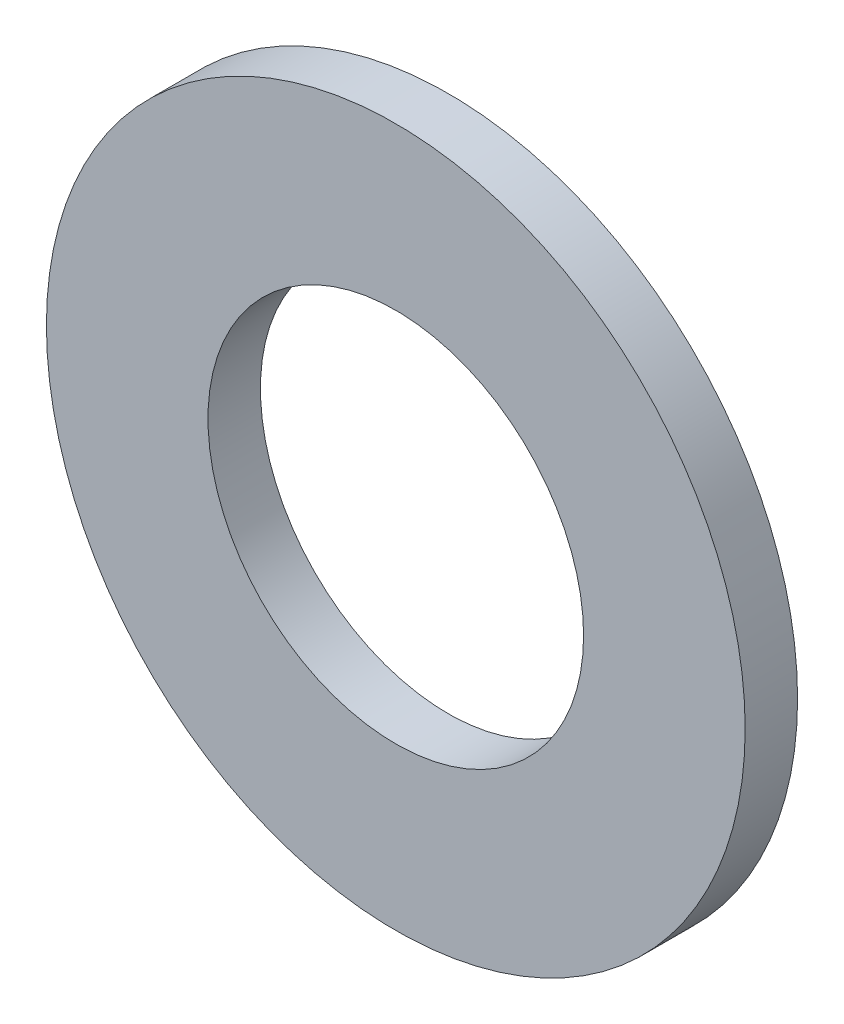
SolidWorks part; units mm, degrees
ref_plane "Front Plane" through (0, 0, 0) normal (0, 0, 1) x (1, 0, 0)
ref_plane "Top Plane" through (0, 0, 0) normal (0, 1, 0) x (1, 0, 0)
ref_plane "Right Plane" through (0, 0, 0) normal (1, 0, 0) x (0, 0, -1)
sketch "Sketch1" plane through (0, 0, 0) normal (0, 0, 1) x (1, 0, 0)
  circle A0 centre (0, 0) radius 4
  circle A1 centre (0, 0) radius 2.15
  point P5 (0, -4)
  dimension "OD" = 8
  dimension "ID" = 4.3
sketch "Sketch2" plane through (0, 0, 0) normal (1, 0, 0) x (0, 0, -1)
  line L0 (-0.3, 0) -> (0.3, 0) construction
  point P0 (-0.3, -4)
  point P4 (0, 0)
  point P6 (0.3, -4)
  dimension "Thickness Range" = 0.6
sketch "Sketch3" plane through (0, 0, 0) normal (0, 0, 1) x (1, 0, 0)
  circle A0 centre (0, 0) radius 4 construction
  circle A1 centre (0, 0) radius 2.15 construction
  circle A2 centre (0, 0) radius 4
  circle A3 centre (0, 0) radius 2.15
extrude "Boss-Extrude1" add sketch "Sketch3" along normal up to vertex (0.3 mm away) and the other way up to vertex (0.3 mm away) up to point (0, -4, 0.3) other way up to point (0, -4, -0.3)
